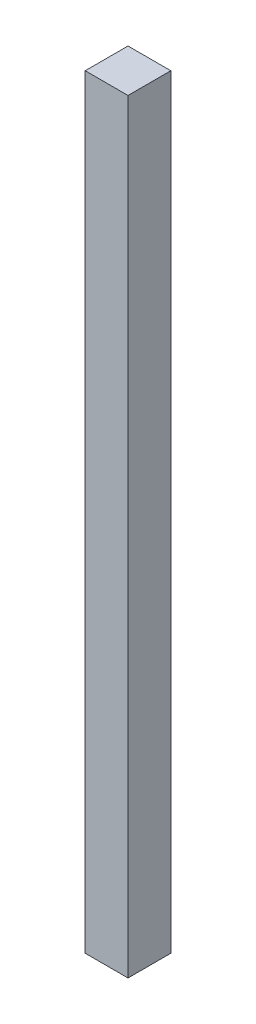
SolidWorks part; units mm, degrees
ref_plane "Front Plane" through (0, 0, 0) normal (0, 0, 1) x (1, 0, 0)
ref_plane "Top Plane" through (0, 0, 0) normal (0, 1, 0) x (1, 0, 0)
ref_plane "Right Plane" through (0, 0, 0) normal (1, 0, 0) x (0, 0, -1)
sketch "Sketch1" plane through (0, 0, 0) normal (0, 1, 0) x (1, 0, 0)
  line L1 (0, 0) -> (25.4, 0)
  line L2 (0, 0) -> (0, 25.4)
  line L3 (0, 25.4) -> (25.4, 25.4)
  line L4 (25.4, 0) -> (25.4, 25.4)
  dimension "D1" = 25.4
  dimension "D2" = 25.4
extrude "Boss-Extrude1" add sketch "Sketch1" along normal blind 453.39
